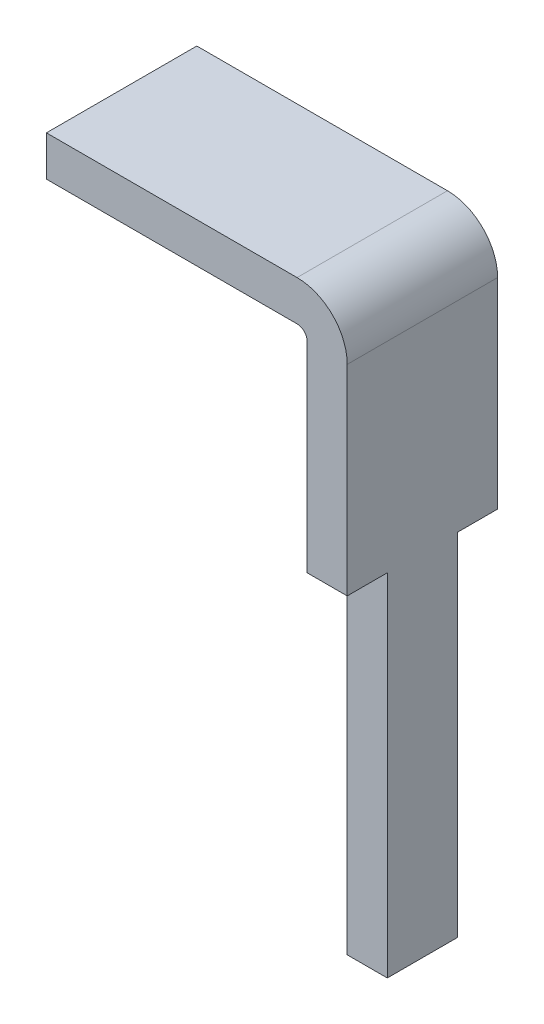
SolidWorks part; units mm, degrees
ref_plane "Front Plane" through (0, 0, 0) normal (0, 0, 1) x (1, 0, 0)
ref_plane "Top Plane" through (0, 0, 0) normal (0, 1, 0) x (1, 0, 0)
ref_plane "Right Plane" through (0, 0, 0) normal (1, 0, 0) x (0, 0, -1)
sketch "Sketch1" plane through (0, 0, 0) normal (0, 0, 1) x (1, 0, 0)
  line L0 (0, 0) -> (2.5, 0)
  line L1 (3, -0.5) -> (3, -6)
  line L2 (0, -0.4) -> (2.5, -0.4)
  line L3 (2.6, -0.5) -> (2.6, -6)
  line L4 (0, 0) -> (0, -0.4)
  line L5 (2.6, -6) -> (3, -6)
  arc A0 (2.5, 0) -> (3, -0.5) centre (2.5, -0.5) cw
  arc A1 (2.5, -0.4) -> (2.6, -0.5) centre (2.5, -0.5) cw
  point P6 (3, 0)
  dimension "D3" = 0.5
  dimension "D1" = 3
  dimension "D2" = 6
  dimension "D4" = 0.4
extrude "Boss-Extrude1" add sketch "Sketch1" along normal blind 1.5
sketch "Sketch2" plane through (3, 0, 0) normal (1, 0, 0) x (0, 0, -1)
  line L0 (-0.75, -0.7454) -> (-0.75, -6) construction
  line L1 (-1.5, -6) -> (0, -6) construction
  line L2 (0, -6) -> (-0.4, -6)
  line L3 (-1.5, -6) -> (-1.1, -6)
  line L4 (-1.5, -6) -> (-1.5, -2.5)
  line L5 (-1.5, -2.5) -> (-1.1, -2.5)
  line L6 (-1.1, -6) -> (-1.1, -2.5)
  line L7 (0, -6) -> (0, -2.5)
  line L8 (-0.4, -6) -> (-0.4, -2.5)
  line L9 (0, -2.5) -> (-0.4, -2.5)
  dimension "D1" = 3.5
  dimension "D2" = 0.35
extrude "Cut-Extrude1" cut sketch "Sketch2" against normal up to next
